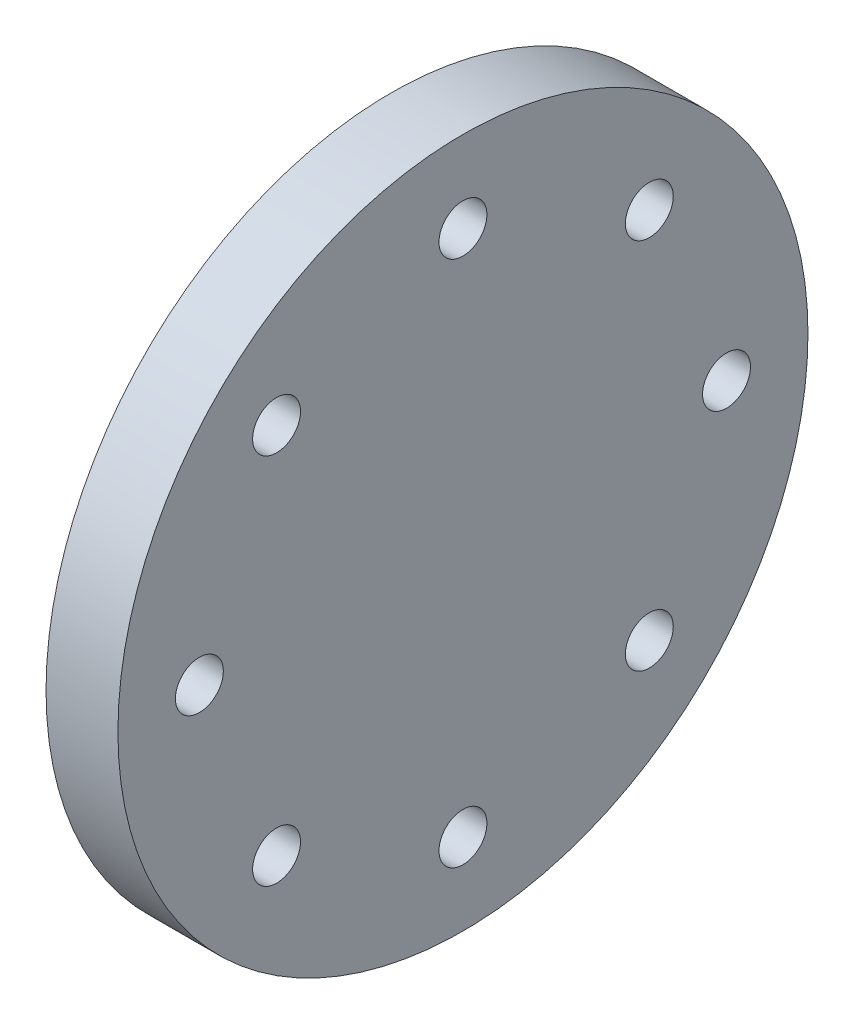
SolidWorks part; units mm, degrees
ref_plane "Front Plane" through (0, 0, 0) normal (0, 0, 1) x (1, 0, 0)
ref_plane "Top Plane" through (0, 0, 0) normal (0, 1, 0) x (1, 0, 0)
ref_plane "Right Plane" through (0, 0, 0) normal (1, 0, 0) x (0, 0, -1)
sketch "Sketch2" plane through (0, 0, 0) normal (1, 0, 0) x (0, 0, -1)
  circle A0 centre (0, 0) radius 72
  circle A1 centre (0, 55) radius 5
  circle A2 centre (38.8909, 38.8909) radius 5
  circle A3 centre (55, 0) radius 5
  circle A4 centre (38.8909, -38.8909) radius 5
  circle A5 centre (0, -55) radius 5
  circle A6 centre (-38.8909, -38.8909) radius 5
  circle A7 centre (-55, 0) radius 5
  circle A8 centre (-38.8909, 38.8909) radius 5
  point P22 (0, 0)
  dimension "D1" = 8
extrude "Boss-Extrude1" add sketch "Sketch2" along normal blind 15
sketch "Sketch3" plane through (0, 0, 0) normal (-1, 0, 0) x (0, 0, 1)
  line L0 (0, 0) -> (0, -45.521)
  point P6 (0, 0)
